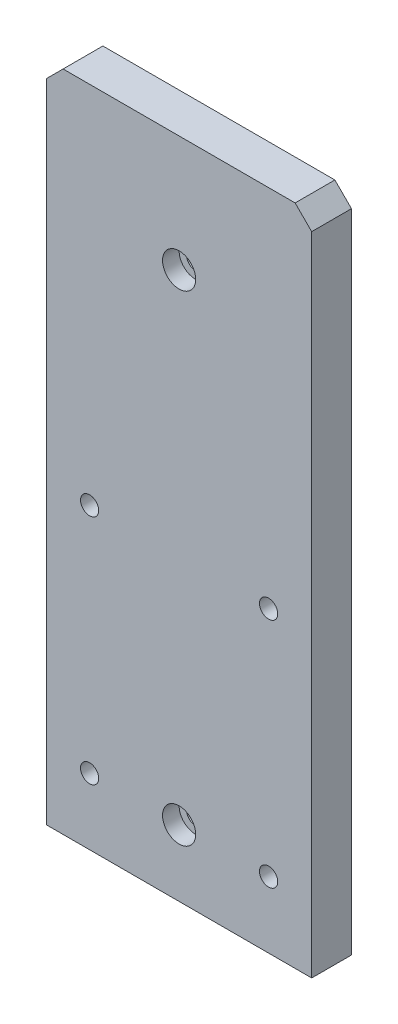
SolidWorks part; units mm, degrees
ref_plane "Front" through (0, 0, 0) normal (0, 0, 1) x (1, 0, 0)
ref_plane "Top" through (0, 0, 0) normal (0, 1, 0) x (1, 0, 0)
ref_plane "Right" through (0, 0, 0) normal (1, 0, 0) x (0, 0, -1)
sketch "Sketch1" plane through (0, 0, 0) normal (0, 0, 1) x (1, 0, 0)
  line L0 (0, 122.1866) -> (0, -10.5895) construction
  line L1 (-40, 0) -> (40, 0)
  line L2 (-40, 0) -> (-40, 195)
  line L3 (-35, 200) -> (35, 200)
  line L4 (40, 0) -> (40, 195)
  line L5 (-35, 200) -> (-40, 195)
  line L6 (35, 200) -> (40, 195)
  dimension "D1" = 80
  dimension "D2" = 200
  dimension "D3" = 5
  dimension "D4" = 5
extrude "Boss-Extrude1" add sketch "Sketch1" along normal blind 12
hole_wizard "CBORE for M5 Socket Head Cap Screw1" positions "Sketch3" profile "Sketch2" counterbore size "M5" standard "JIS" end condition through all
sketch "Sketch3" plane through (0, 0, 12) normal (0, 0, 1) x (1, 0, 0)
  line L0 (-40, 0) -> (40, 0) construction
  point P0 (0, 20)
  point P1 (0, 165)
  dimension "D1" = 20
  dimension "D2" = 145
sketch "Sketch2" plane through (0, 20, 12) normal (1, 0, 0) x (0, -1, 0)
  line L0 (0, 0) -> (0, 12)
  line L1 (0, 12) -> (2.75, 12)
  line L3 (2.75, 12) -> (2.75, 5)
  line L4 (2.75, 5) -> (5, 5)
  line L5 (5, 5) -> (5, 0)
  line L7 (5, 0) -> (0, 0)
  line L11 (0, -6.35) -> (0, 107.95) construction
  dimension "通し穴の直径" = 5.5
  dimension "通し穴の深さ" = 12
  dimension "座ぐり穴の直径" = 10
  dimension "座ぐり穴の深さ" = 5
hole_wizard "M5x0.8 Tapped Hole1" positions "Sketch5" profile "Sketch4" tap size "M5x0.8" standard "JIS"
sketch "Sketch5" plane through (0, 0, 0) normal (0, -1, 0) x (1, 0, 0)
  line L0 (-40, 0) -> (40, 0) construction
  line L2 (0, 17.1703) -> (0, -4.6288) construction
  point P0 (-25, 6)
  point P1 (25, 6)
  dimension "D1" = 6
  dimension "D3" = 50
sketch "Sketch4" plane through (-25, 0, 6) normal (1, 0, 0) x (0, 0, -1)
  line L0 (0, 0) -> (0, 15.2618)
  line L1 (0, 15.2618) -> (2.1, 14)
  line L2 (2.1, 14) -> (2.1, 0)
  line L5 (2.1, 0) -> (0, 0)
  line L10 (0, 15.2618) -> (-2.1, 14) construction
  line L11 (0, -6.35) -> (0, 107.95) construction
  dimension "ねじ下穴ﾄﾞﾘﾙ直径" = 4.2
  dimension "ねじ下穴ﾄﾞﾘﾙの深さ" = 14
  dimension "ﾄﾞﾘﾙ角度" = 118
cosmetic thread "Hole Thread1" parameters "D1"=10, "D2"=5
cosmetic thread "Hole Thread2" parameters "D1"=10, "D2"=5
sketch "Sketch6" plane through (0, 0, 0) normal (0, 1, 0) x (1, 0, 0)
  line L0 (0, -14.2452) -> (0, 9.5784) construction
  line L1 (-40, 0) -> (40, 0) construction
  circle A0 centre (33, -6) radius 2
  circle A1 centre (-33, -6) radius 2
  dimension "D3" = 4
  dimension "D1" = 6
  dimension "D2" = 66
extrude "Cut-Extrude1" cut sketch "Sketch6" along normal blind 8
hole_wizard "CBORE for M5 Socket Head Cap Screw2" positions "Sketch8" profile "Sketch7" counterbore size "M5" standard "JIS" end condition through all
sketch "Sketch8" plane through (0, 0, 0) normal (0, 0, -1) x (-1, 0, 0)
  line L0 (0, 107.2347) -> (0, -4.6331) construction
  line L2 (-52.0694, 55) -> (52.883, 55) construction
  line L4 (-35, 200) -> (35, 200) construction
  point P0 (27, 20)
  point P1 (27, 90)
  point P3 (-27, 90)
  point P5 (-27, 20)
  dimension "D1" = 70
  dimension "D2" = 54
  dimension "D3" = 55
  dimension "D4" = 110
sketch "Sketch7" plane through (-27, 20, 0) normal (1, 0, 0) x (0, 1, 0)
  line L0 (0, 0) -> (0, 12)
  line L1 (0, 12) -> (2.75, 12)
  line L3 (2.75, 12) -> (2.75, 5)
  line L4 (2.75, 5) -> (5, 5)
  line L5 (5, 5) -> (5, 0)
  line L7 (5, 0) -> (0, 0)
  line L11 (0, -6.35) -> (0, 107.95) construction
  dimension "通し穴の直径" = 5.5
  dimension "通し穴の深さ" = 12
  dimension "座ぐり穴の直径" = 10
  dimension "座ぐり穴の深さ" = 5
